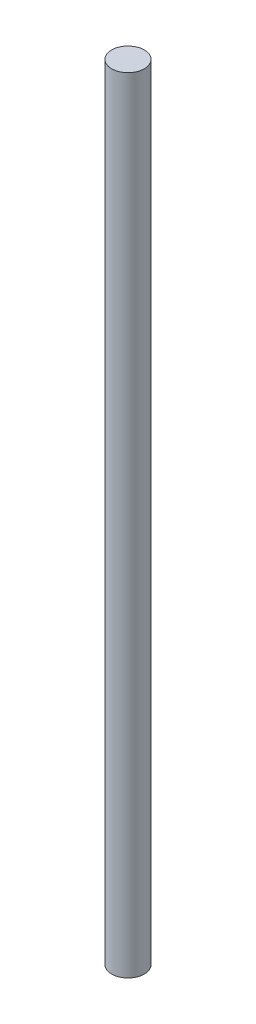
SolidWorks part; units mm, degrees
material "6061 Alloy"
ref_plane "Front Plane" through (0, 0, 0) normal (0, 0, 1) x (1, 0, 0)
ref_plane "Top Plane" through (0, 0, 0) normal (0, 1, 0) x (1, 0, 0)
ref_plane "Right Plane" through (0, 0, 0) normal (1, 0, 0) x (0, 0, -1)
sketch "Sketch1" plane through (0, 0, 0) normal (0, 1, 0) x (1, 0, 0)
  circle A0 centre (0, 0) radius 12.7
  dimension "D1" = 25.4
extrude "Boss-Extrude1" add sketch "Sketch1" along normal blind 609.6
